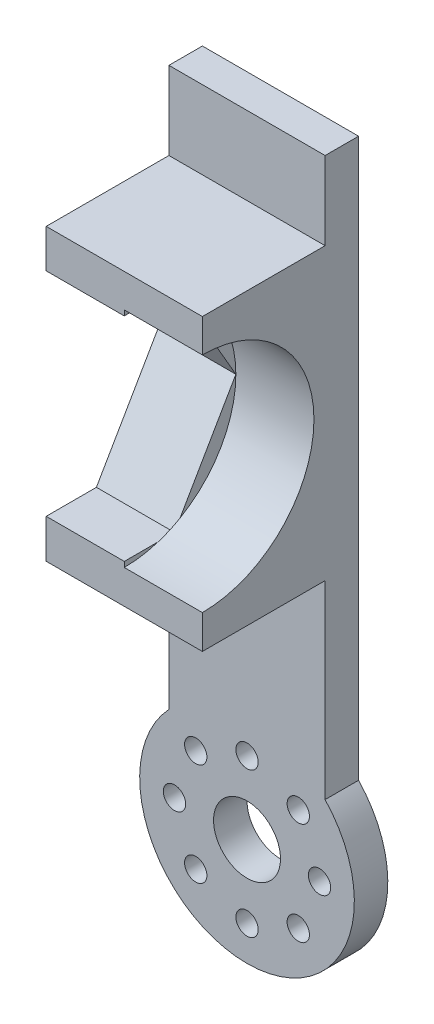
SolidWorks part; units mm, degrees
ref_plane "前视基准面" through (0, 0, 0) normal (0, 0, 1) x (1, 0, 0)
ref_plane "上视基准面" through (0, 0, 0) normal (0, 1, 0) x (1, 0, 0)
ref_plane "右视基准面" through (0, 0, 0) normal (1, 0, 0) x (0, 0, -1)
sketch "草图1" plane through (0, 0, 0) normal (0, 0, 1) x (1, 0, 0)
  line L1 (-7, -6.6001) -> (7, -6.6001)
  line L2 (-7, -6.6001) -> (-7, 6.6001)
  line L3 (-7, 6.6001) -> (7, 6.6001)
  line L4 (7, -6.6001) -> (7, 6.6001)
  line L5 (-7, -6.6001) -> (7, 6.6001) construction
  line L6 (-7, 6.6001) -> (7, -6.6001) construction
  line L7 (-7, 6.6001) -> (7, 6.6001)
  line L8 (-7, 6.6001) -> (-7, 56.6001)
  line L9 (-7, 56.6001) -> (7, 56.6001)
  line L10 (7, 6.6001) -> (7, 56.6001)
  circle A0 centre (0, 0) radius 9.6209
  dimension "D1" = 14
  dimension "D2" = 50
extrude "凸台-拉伸1" add sketch "草图1" along normal blind 3 contours A0 L10 L9 L8
sketch "草图3" plane through (0, 0, 3) normal (0, 0, 1) x (1, 0, 0)
  line L0 (0, 56.6001) -> (0, 46.6001)
  line L1 (-7, 56.6001) -> (7, 56.6001) construction
  line L2 (0, 46.6001) -> (0, 36.6001)
  line L3 (-2, 48.6001) -> (2, 48.6001)
  line L4 (-2, 48.6001) -> (-2, 44.6001)
  line L5 (-2, 44.6001) -> (2, 44.6001)
  line L6 (2, 48.6001) -> (2, 44.6001)
  line L7 (-2, 48.6001) -> (2, 44.6001) construction
  line L8 (-2, 44.6001) -> (2, 48.6001) construction
  line L9 (0, 36.6001) -> (0, 26.6001)
  line L10 (-2, 38.6001) -> (2, 38.6001)
  line L11 (-2, 38.6001) -> (-2, 34.6001)
  line L12 (-2, 34.6001) -> (2, 34.6001)
  line L13 (2, 38.6001) -> (2, 34.6001)
  line L14 (-2, 38.6001) -> (2, 34.6001) construction
  line L15 (-2, 34.6001) -> (2, 38.6001) construction
  line L17 (-2, 28.6001) -> (2, 28.6001)
  line L18 (-2, 28.6001) -> (-2, 24.6001)
  line L19 (-2, 24.6001) -> (2, 24.6001)
  line L20 (2, 28.6001) -> (2, 24.6001)
  line L21 (-2, 28.6001) -> (2, 24.6001) construction
  line L22 (-2, 24.6001) -> (2, 28.6001) construction
  dimension "D1" = 10
  dimension "D2" = 4
  dimension "D3" = 4
  dimension "D4" = 10
  dimension "D5" = 4
  dimension "D6" = 10
  dimension "D7" = 4
extrude "切除-拉伸2" cut sketch "草图3" against normal blind 3 flip side to cut
sketch "草图4" plane through (0, 0, 3) normal (0, 0, 1) x (1, 0, 0)
  circle A0 centre (0, 0) radius 3
extrude "切除-拉伸3" cut sketch "草图4" against normal blind 10
sketch "草图5" plane through (0, 0, 0) normal (0, 0, -1) x (-1, 0, 0)
  line L0 (0, 0) -> (0, 6.5)
  circle A0 centre (0, 6.5) radius 1
  dimension "D1" = 6.5
extrude "切除-拉伸4" cut sketch "草图5" against normal blind 10
sketch "草图6" plane through (0, 0, 0) normal (0, 0, -1) x (-1, 0, 0)
  line L1 (-2, 38.6001) -> (2, 38.6001)
  line L2 (-2, 38.6001) -> (-2, 34.6001)
  line L3 (-2, 34.6001) -> (2, 34.6001)
  line L4 (2, 38.6001) -> (2, 34.6001)
extrude "凸台-拉伸3" add sketch "草图6" against normal up to surface (3 mm away) up to face at (1, 6.5, 3)
sketch "草图7" plane through (0, 0, 0) normal (0, 0, -1) x (-1, 0, 0)
  line L0 (0, 28.6001) -> (0, 44.6001)
  line L1 (2, 28.6001) -> (-2, 28.6001) construction
  line L2 (2, 44.6001) -> (-2, 44.6001) construction
  circle A0 centre (0, 36.6001) radius 2
extrude "切除-拉伸5" cut sketch "草图7" against normal blind 10 contours L0 A0 | L0 A0
cosmetic thread "装饰螺纹线1" parameters "D2"=5
pattern_circular "阵列(圆周)1" count 8 over 360 about axis through (0, 0, 0) along (0, 0, 1) of "切除-拉伸4"
sketch "草图8" plane through (0, 0, 3) normal (0, 0, 1) x (1, 0, 0)
  line L0 (-2, 44.6001) -> (2, 44.6001) construction
  line L1 (2, 48.6001) -> (2, 44.6001) construction
  line L2 (-2, 48.6001) -> (2, 48.6001) construction
  line L3 (-7, 56.6001) -> (-7, 6.6001)
  line L4 (7, 6.6001) -> (7, 56.6001)
  line L5 (7, 56.6001) -> (-7, 56.6001)
  line L6 (-7, 56.6001) -> (-7, 6.6001)
  line L7 (7, 6.6001) -> (7, 56.6001)
  line L8 (7, 56.6001) -> (-7, 56.6001)
  line L9 (-2, 48.6001) -> (-2, 44.6001) construction
  line L10 (-2, 44.6001) -> (2, 44.6001)
  line L11 (2, 48.6001) -> (2, 44.6001)
  line L12 (-2, 48.6001) -> (2, 48.6001)
  line L13 (-2, 48.6001) -> (-2, 44.6001)
  line L14 (-2, 24.6001) -> (2, 24.6001) construction
  line L15 (2, 28.6001) -> (2, 24.6001) construction
  line L16 (-2, 28.6001) -> (2, 28.6001) construction
  line L17 (-2, 28.6001) -> (-2, 24.6001) construction
  line L18 (-2, 24.6001) -> (2, 24.6001)
  line L19 (2, 28.6001) -> (2, 24.6001)
  line L20 (-2, 28.6001) -> (2, 28.6001)
  line L21 (-2, 28.6001) -> (-2, 24.6001)
  circle A0 centre (0, 36.6001) radius 2 construction
  arc A1 (-7, 6.6001) -> (7, 6.6001) centre (0, 0) ccw
  arc A2 (-7, 6.6001) -> (7, 6.6001) centre (0, 0) ccw
  circle A3 centre (0, 36.6001) radius 2
  circle A4 centre (-4.5962, -4.5962) radius 1 construction
  circle A5 centre (-6.5, 0) radius 1 construction
  circle A6 centre (0, -6.5) radius 1 construction
  circle A7 centre (4.5962, -4.5962) radius 1 construction
  circle A8 centre (6.5, 0) radius 1 construction
  circle A9 centre (4.5962, 4.5962) radius 1 construction
  circle A10 centre (-4.5962, 4.5962) radius 1 construction
  circle A11 centre (0, 6.5) radius 1 construction
  circle A12 centre (0, 0) radius 3 construction
  circle A13 centre (-4.5962, -4.5962) radius 1
  circle A14 centre (-6.5, 0) radius 1
  circle A15 centre (0, -6.5) radius 1
  circle A16 centre (4.5962, -4.5962) radius 1
  circle A17 centre (6.5, 0) radius 1
  circle A18 centre (4.5962, 4.5962) radius 1
  circle A19 centre (-4.5962, 4.5962) radius 1
  circle A20 centre (0, 6.5) radius 1
  circle A21 centre (0, 0) radius 3
  dimension "D1" = 0
sketch "草图9" plane through (0, 0, 3) normal (0, 0, 1) x (1, 0, 0)
  line L0 (-7, 56.6001) -> (-7, 6.6001) construction
  line L1 (-7, 49.6001) -> (7, 49.6001)
  line L2 (-7, 49.6001) -> (-7, 23.6001)
  line L3 (-7, 23.6001) -> (7, 23.6001)
  line L4 (7, 49.6001) -> (7, 23.6001)
  line L5 (7, 6.6001) -> (7, 56.6001) construction
  line L7 (-2, 48.6001) -> (2, 48.6001) construction
  dimension "D1" = 26
  dimension "D2" = 1
extrude "凸台-拉伸4" add sketch "草图9" along normal blind 11
sketch "草图10" plane through (-7, 0, 0) normal (-1, 0, 0) x (0, 0, 1)
  line L2 (4, 36.6186) -> (9.5, 27.0923)
  line L3 (9.5, 27.0923) -> (14, 27.0923)
  line L6 (14, 46.1449) -> (9.5, 46.1449)
  line L7 (9.5, 46.1449) -> (4, 36.6186)
  line L8 (14, 46.1449) -> (14, 27.0923)
  line L10 (22.8471, 42.0796) -> (20.3471, 46.4097) [skipped]
  line L11 (21.3104, 28.496) -> (23.8104, 32.8262) [skipped]
  line L12 (3, 38.6001) -> (3, 34.6001) construction
  line L13 (14, 49.6001) -> (14, 23.6001) construction
  dimension "D1" = 1
extrude "切除-拉伸8" cut sketch "草图10" against normal blind 7 contours L7 L2 L3 L8 L6
sketch "草图11" plane through (0, 0, 0) normal (-1, 0, 0) x (0, 0, 1)
  line L0 (14, 46.1449) -> (14, 27.0923) construction
  circle A0 centre (14, 36.6186) radius 10
  dimension "D1" = 20
extrude "切除-拉伸9" cut sketch "草图11" against normal blind 7
sketch "草图12" plane through (0, 0, 3) normal (0, 0, -1) x (-1, 0, 0)
  line L4 (2, 44.6001) -> (2, 48.6001)
  line L5 (2, 48.6001) -> (-2, 48.6001)
  line L6 (-2, 48.6001) -> (-2, 44.6001)
  line L7 (-2, 44.6001) -> (2, 44.6001)
  line L8 (2, 44.6001) -> (2, 48.6001)
  line L9 (2, 48.6001) -> (-2, 48.6001)
  line L10 (-2, 48.6001) -> (-2, 44.6001)
  line L11 (-2, 44.6001) -> (2, 44.6001)
  line L12 (2, 24.6001) -> (2, 28.6001)
  line L13 (2, 28.6001) -> (-2, 28.6001)
  line L14 (-2, 28.6001) -> (-2, 24.6001)
  line L15 (-2, 24.6001) -> (2, 24.6001)
  line L16 (2, 24.6001) -> (2, 28.6001)
  line L17 (2, 28.6001) -> (-2, 28.6001)
  line L18 (-2, 28.6001) -> (-2, 24.6001)
  line L19 (-2, 24.6001) -> (2, 24.6001)
  dimension "D1" = 0
  dimension "D2" = 0
extrude "切除-拉伸10" cut sketch "草图12" against normal blind 1
